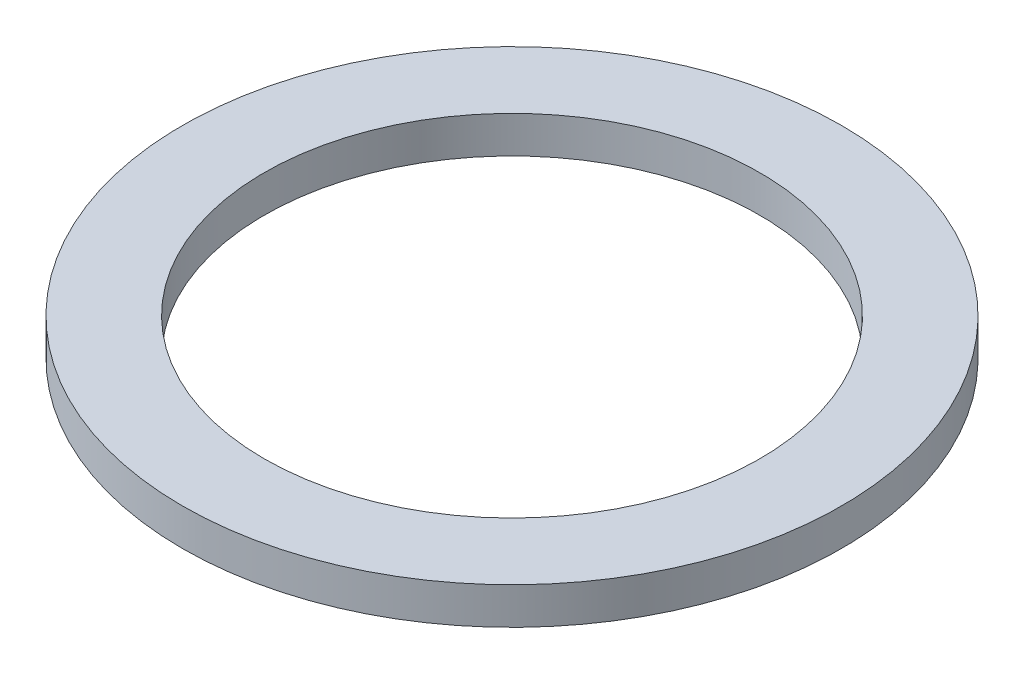
SolidWorks part; units mm, degrees
ref_plane "Front Plane" through (0, 0, 0) normal (0, 0, 1) x (1, 0, 0)
ref_plane "Top Plane" through (0, 0, 0) normal (0, 1, 0) x (1, 0, 0)
ref_plane "Right Plane" through (0, 0, 0) normal (1, 0, 0) x (0, 0, -1)
sketch "Sketch1" plane through (0, 0, 0) normal (0, 1, 0) x (1, 0, 0)
  circle A0 centre (0, 0) radius 2.3876
  circle A1 centre (0, 0) radius 3.175
  dimension "D1" = 4.7752
  dimension "D2" = 6.35
extrude "Boss-Extrude1" add sketch "Sketch1" along normal blind 0.3556
